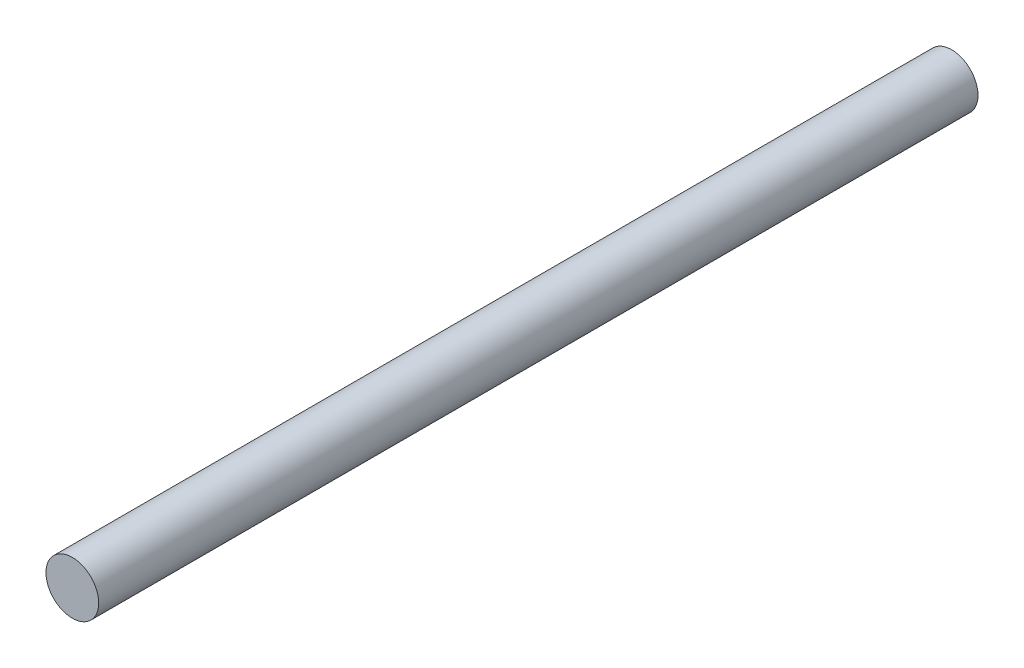
SolidWorks part; units mm, degrees
ref_plane "Front Plane" through (0, 0, 0) normal (0, 0, 1) x (1, 0, 0)
ref_plane "Top Plane" through (0, 0, 0) normal (0, 1, 0) x (1, 0, 0)
ref_plane "Right Plane" through (0, 0, 0) normal (1, 0, 0) x (0, 0, -1)
sketch "Sketch1" plane through (0, 0, 0) normal (0, 0, 1) x (1, 0, 0)
  circle A0 centre (0, 0) radius 15
  dimension "D1" = 30
extrude "Boss-Extrude1" add sketch "Sketch1" along normal blind 500
